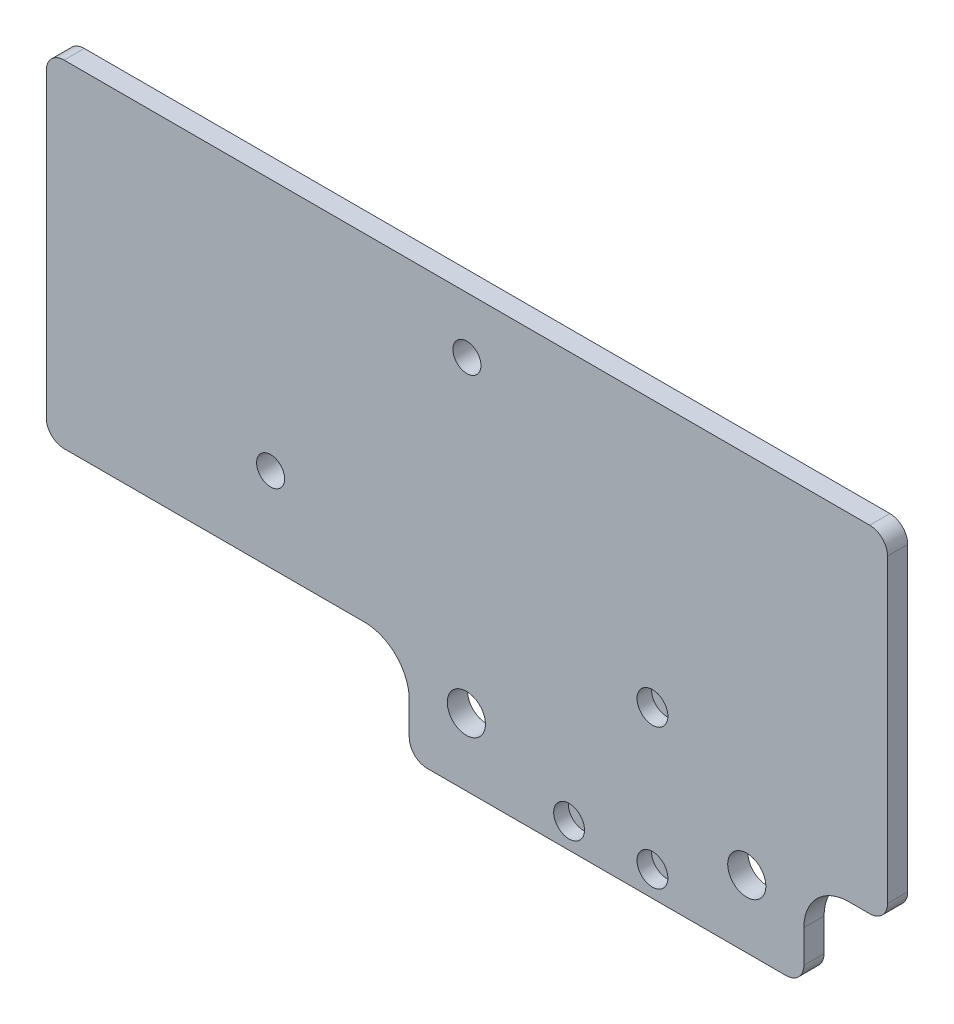
SolidWorks part; units mm, degrees
ref_plane "Front Plane" through (0, 0, 0) normal (0, 0, 1) x (1, 0, 0)
ref_plane "Top Plane" through (0, 0, 0) normal (0, 1, 0) x (1, 0, 0)
ref_plane "Right Plane" through (0, 0, 0) normal (1, 0, 0) x (0, 0, -1)
sketch "Sketch1" plane through (0, 0, 0) normal (0, 0, 1) x (1, 0, 0)
  line L0 (24.9, -77) -> (24.9, -77.8546) construction
  line L1 (-0.1, -65) -> (49.9, -65) construction
  line L28 (71.82, 0) -> (-71.82, 0)
  line L29 (-75, -3.18) -> (-75, -56.82)
  line L30 (-71.82, -60) -> (-18.28, -60)
  line L31 (-10.28, -68) -> (-10.28, -73.82)
  line L35 (-7.1, -77) -> (56.9, -77)
  line L39 (60.08, -73.82) -> (60.08, -68)
  line L40 (68.08, -60) -> (71.82, -60)
  line L41 (75, -56.82) -> (75, -3.18)
  circle A0 centre (-35, -45) radius 2.5
  circle A2 centre (0, -10) radius 2.5
  circle A3 centre (-0.1, -65) radius 3.4
  circle A4 centre (49.9, -65) radius 3.4
  circle A6 centre (33.08, -72.5) radius 2.75
  circle A7 centre (18.22, -72.5) radius 2.75
  circle A8 centre (33.08, -47.5) radius 2.75
  arc A20 (75, -3.18) -> (71.82, 0) centre (71.82, -3.18) ccw
  arc A21 (-71.82, 0) -> (-75, -3.18) centre (-71.82, -3.18) ccw
  arc A22 (-75, -56.82) -> (-71.82, -60) centre (-71.82, -56.82) ccw
  arc A23 (-10.28, -68) -> (-18.28, -60) centre (-18.28, -68) ccw
  arc A24 (-10.28, -73.82) -> (-7.1, -77) centre (-7.1, -73.82) ccw
  arc A27 (56.9, -77) -> (60.08, -73.82) centre (56.9, -73.82) ccw
  arc A28 (68.08, -60) -> (60.08, -68) centre (68.08, -68) ccw
  arc A29 (71.82, -60) -> (75, -56.82) centre (71.82, -56.82) ccw
  point P0 (0, 0)
  point P24 (24.9, -65)
  dimension "D6" = 3.18
  dimension "D7" = 8
  dimension "D9" = 60
  dimension "D13" = 5
  dimension "D15" = 40
  dimension "D16" = 27
  dimension "D17" = 6.8
  dimension "D8" = 12
  dimension "D11" = 75
  dimension "D12" = 50
  dimension "D3" = 50
  dimension "D10" = 5.5
  dimension "D18" = 28.5
  dimension "D19" = 4.5
  dimension "D20" = 29.5
  dimension "D1" = 150
  dimension "D2" = 64
  dimension "D4" = 5.82
  dimension "D5" = 50.1
  dimension "D14" = 15
extrude "Boss-Extrude1" add sketch "Sketch1" along normal blind 3.6
sketch "Sketch3" plane through (0, 0, 0) normal (0, 0, -1) x (-1, 0, 0)
  line L0 (7.1, -77) -> (-56.9, -77) construction
  line L1 (-37.08, -42.5) -> (-14.22, -42.5)
  line L2 (-37.08, -42.5) -> (-37.08, -77)
  line L3 (-37.08, -77) -> (-14.22, -77)
  line L4 (-14.22, -42.5) -> (-14.22, -77)
  circle A1 centre (-33.08, -47.5) radius 2.75 construction
  circle A2 centre (-33.08, -72.5) radius 2.75 construction
  circle A3 centre (-18.22, -72.5) radius 2.75 construction
  dimension "D2" = 4
  dimension "D3" = 4
  dimension "D1" = 5
extrude "Boss-Extrude3" add sketch "Sketch3" against normal blind 1
